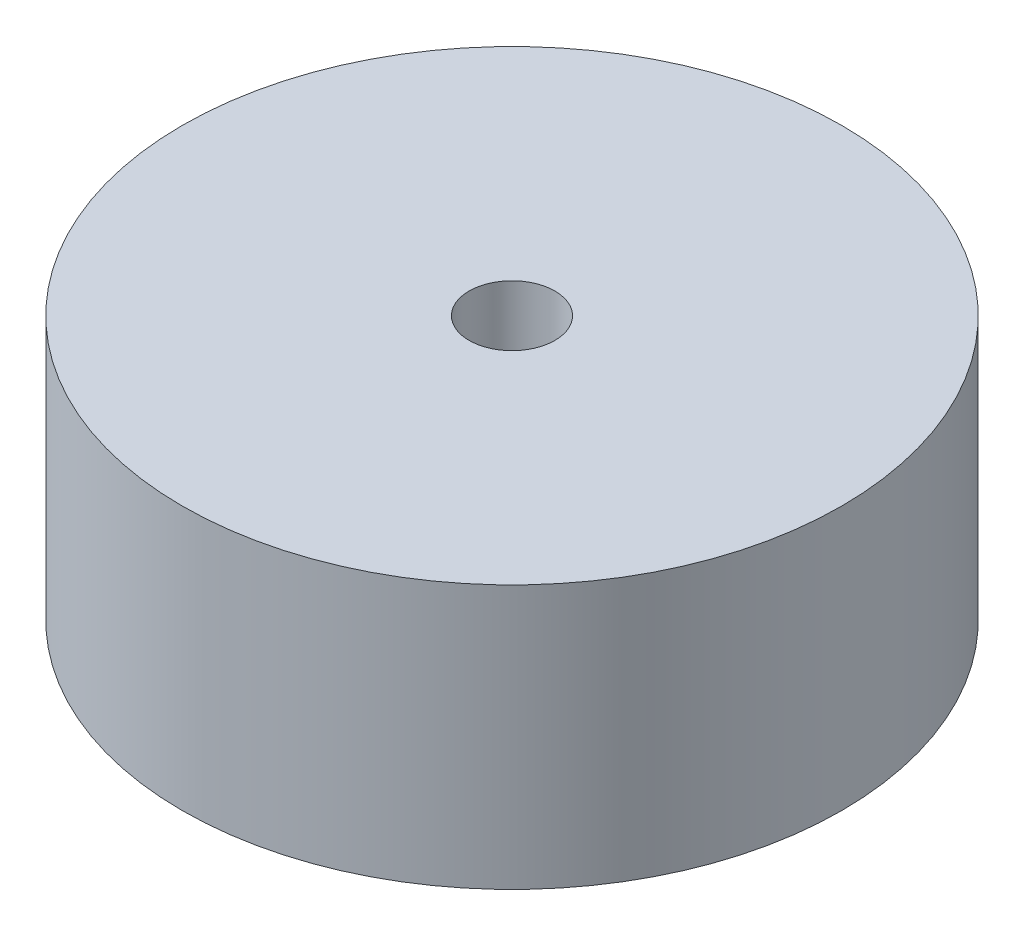
SolidWorks part; units mm, degrees
ref_plane "Front Plane" through (0, 0, 0) normal (0, 0, 1) x (1, 0, 0)
ref_plane "Top Plane" through (0, 0, 0) normal (0, 1, 0) x (1, 0, 0)
ref_plane "Right Plane" through (0, 0, 0) normal (1, 0, 0) x (0, 0, -1)
sketch "Sketch1" plane through (0, 0, 0) normal (0, 1, 0) x (1, 0, 0)
  circle A0 centre (0, 0) radius 50
extrude "Boss-Extrude1" add sketch "Sketch1" along normal blind 40
hole_wizard "Ø13.0 (13) Diameter Hole1" positions "Sketch3" profile "Sketch2" hole size "Ø13.0" standard "ANSI Metric" end condition through all
sketch "Sketch3" plane through (0, 0, 0) normal (0, -1, 0) x (-1, 0, 0)
  point P0 (0, 0)
sketch "Sketch2" plane through (0, 0, 0) normal (1, 0, 0) x (0, 0, -1)
  line L0 (0, 0) -> (0, 40)
  line L1 (0, 40) -> (6.5, 40)
  line L2 (6.5, 40) -> (6.5, 0)
  line L5 (6.5, 0) -> (0, 0)
  line L11 (0, -6.35) -> (0, 107.95) construction
  dimension "Thru Hole Dia." = 13
  dimension "Thru Hole Depth" = 40
